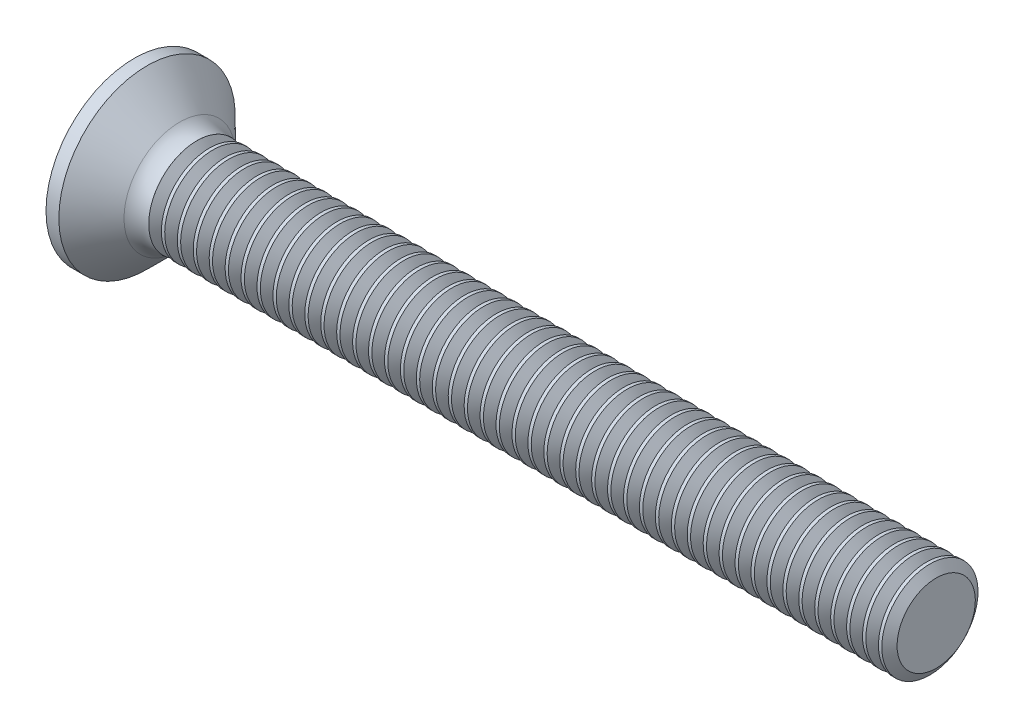
SolidWorks part; units mm, degrees
revolve "Base-Revolve" add sketch "BodySke"
sketch "BodySke" plane through (0, 0, 0) normal (0, 0, 1) x (1, 0, 0)
  line L0 (0, 0) -> (0, 2.75)
  line L1 (0, 2.75) -> (0.4, 2.75)
  line L2 (1.65, 1.5) -> (25, 1.5)
  line L3 (25, 1.5) -> (25, 0)
  line L4 (25, 0) -> (0, 0)
  line L5 (-6.35, 0) -> (82.55, 0) construction
  line L6 (1.65, -1.5) -> (25, -1.5) construction
  line L7 (0.4, -2.75) -> (1.65, -1.5) construction
  line L8 (0.4, 2.75) -> (1.65, 1.5)
  line L9 (0, -2.75) -> (0.4, -2.75) construction
  line L10 (2.15, 3.0875) -> (2.15, -6.4375) construction
  line L11 (0, 6.35) -> (0, -3.175) construction
  dimension "Diameter" = 3
  dimension "Length" = 25
  dimension "Head_ht" = 1.65
  dimension "Head_dia" = 5.5
  dimension "Head_ang" = 90
  dimension "D6" = 0.4
  dimension "Advance" = 0.5
  dimension "Thread_nom" = 25
cosmetic thread "ThreadCosmetic" [suppressed]
fillet "Fillet1" radius 0.8 1 edges at (1.65, 0, 1.5)
ref_plane "Plane1" through (0, 0, 0) normal (0, 0, 1) x (1, 0, 0)
ref_plane "Plane2" through (0, 0, 0) normal (0, 1, 0) x (1, 0, 0)
ref_plane "Plane3" through (0, 0, 0) normal (1, 0, 0) x (0, 0, -1)
sketch "Sketch3" plane through (0, 0, 0) normal (-1, 0, 0) x (0, 0, 1)
  line L0 (-0.37, 1.5) -> (0.37, 1.5)
  line L1 (0.37, 1.5) -> (0.37, -1.5)
  line L2 (0.37, -1.5) -> (-0.37, -1.5)
  line L3 (-0.37, -1.5) -> (-0.37, 1.5)
  dimension "Cross_dia" = 3
  dimension "Cross_width" = 0.74
  dimension "D1" = 1.5
  dimension "D2" = 0.37
ref_plane "Plane4" through (2.01, 0, 0) normal (-1, 0, 0) x (0, 0, 1)
sketch "Sketch4" plane through (2.01, 0, 0) normal (-1, 0, 0) x (0, 0, 1)
  line L0 (-0.37, 0.4979) -> (0.37, 0.4979)
  line L3 (0.37, 0.4979) -> (0.37, -0.4979)
  line L4 (0.37, -0.4979) -> (-0.37, -0.4979)
  line L5 (-0.37, -0.4979) -> (-0.37, 0.4979)
  dimension "D2" = 0.9957
  dimension "D1" = 0.74
  dimension "D4" = 0.4979
  dimension "D3" = 0.37
loft "Recess" cut profiles "Sketch3", "Sketch4"
pattern_circular "RecPat" count 2 every 90 about axis through (0, 0, 0) along (1, 0, 0) of "Recess"
sketch "RecCorSke" plane through (0, 0, 0) normal (0, 0, 1) x (1, 0, 0)
  line L0 (-3.175, 0) -> (15.875, 0) construction
  line L2 (0, 0) -> (0, 0.6966)
  line L3 (0, 0.6966) -> (2.01, 0.556)
  line L4 (2.01, 0.556) -> (2.1907, 0)
  line L5 (2.1907, 0) -> (0, 0)
  dimension "Diameter" = 1.112
  dimension "Depth" = 2.01
  dimension "Draft_angle" = 4
  dimension "Bottom_angle" = 18
revolve "RecessCore" cut sketch "RecCorSke" angle 360 about L0
sketch "ThdSchSke" plane through (0, 0, 0) normal (0, 0, 1) x (1, 0, 0)
  line L0 (2.15, -1.2195) -> (1.9536, -1.5)
  line L1 (2.15, -1.2195) -> (2.3464, -1.5)
  line L2 (2.3464, -1.5) -> (2.3464, -1.875)
  line L3 (-3.175, 0) -> (5.1513, 0) construction
  line L5 (2.3464, -1.875) -> (1.9536, -1.875)
  line L6 (1.9536, -1.875) -> (1.9536, -1.5)
  line L7 (0, 2.75) -> (0, -2.75) construction
  dimension "Diameter" = 3
  dimension "Thread_minor" = 2.439
  dimension "Start" = 2.15
revolve "ThreadSchematic" cut sketch "ThdSchSke" angle 360 about L3
pattern_linear "ThdSchPat" count 47 spacing 0.4967 along (1, 0, 0) of "ThreadSchematic"
equation "\"D1@Sketch3\" = \"Cross_dia@Sketch3\" / 2"
equation "\"D2@Sketch3\" = \"Cross_width@Sketch3\" / 2"
equation "\"Depth@RecCorSke\" = \"Cross_depth@Plane4\""
equation "\"D1@Sketch4\" = \"Cross_width@Sketch3\""
equation "\"D2@Sketch4\" = \"Cross_dia@Sketch3\" - 2.0 * \"Cross_depth@Plane4\" * tan(26.5  * 0.017453292)"
equation "\"D3@Sketch4\" = \"D1@Sketch4\" / 2"
equation "\"D4@Sketch4\" = \"D2@Sketch4\" / 2"
equation "\"Thread_length@ThreadCosmetic\" = ((sgn( (\"Length@BodySke\" - \"Advance@BodySke\" * 1.0 - \"Head_ht@BodySke\" ) - \"Thread_nom@BodySke\" )-1)*( (\"Length@BodySke\" - \"Advance@BodySke\" * 1.0 - \"Head_ht@BodySke\" ) - \"Thread_nom@BodySke\" ))/-2+ \"Thread_nom@BodySke\""
equation "\"Thread_minor@ThdSchSke\" = \"Thread_minor@ThreadCosmetic\""
equation "\"Diameter@ThdSchSke\" = \"Diameter@BodySke\""
equation "\"Overcut@ThdSchSke\" = \"Diameter@BodySke\" * 1.25"
equation "\"Start@ThdSchSke\" = 0.000001 + \"Length@BodySke\" - \"Thread_length@ThreadCosmetic\"  '---Countersunk---"
equation "\"Num_threads@ThdSchPat\" = int( \"Thread_length@ThreadCosmetic\" / \"Advance@BodySke\" + 0.999 )  + 1"
equation "\"Advance@ThdSchPat\" = \"Thread_length@ThreadCosmetic\" /  (\"Num_threads@ThdSchPat\" - 1) 'relax it"
